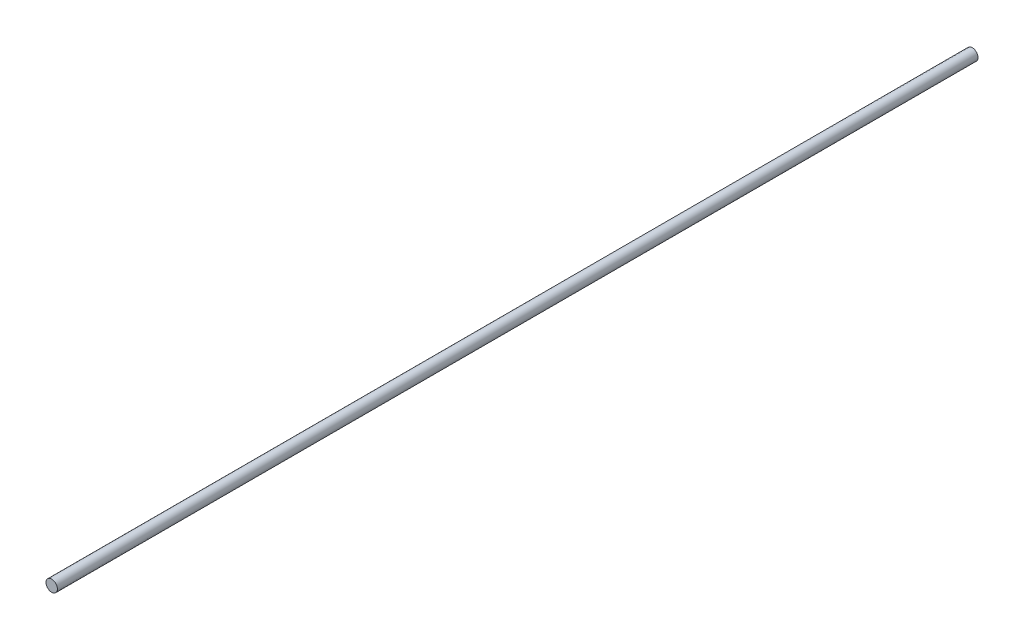
SolidWorks part; units mm, degrees
ref_plane "前视基准面" through (0, 0, 0) normal (0, 0, 1) x (1, 0, 0)
ref_plane "上视基准面" through (0, 0, 0) normal (0, 1, 0) x (1, 0, 0)
ref_plane "右视基准面" through (0, 0, 0) normal (1, 0, 0) x (0, 0, -1)
sketch "草图1" plane through (0, 0, 0) normal (0, 0, 1) x (1, 0, 0)
  circle A0 centre (0, 0) radius 4
  dimension "D1" = 8
extrude "凸台-拉伸1" add sketch "草图1" along normal blind 645
